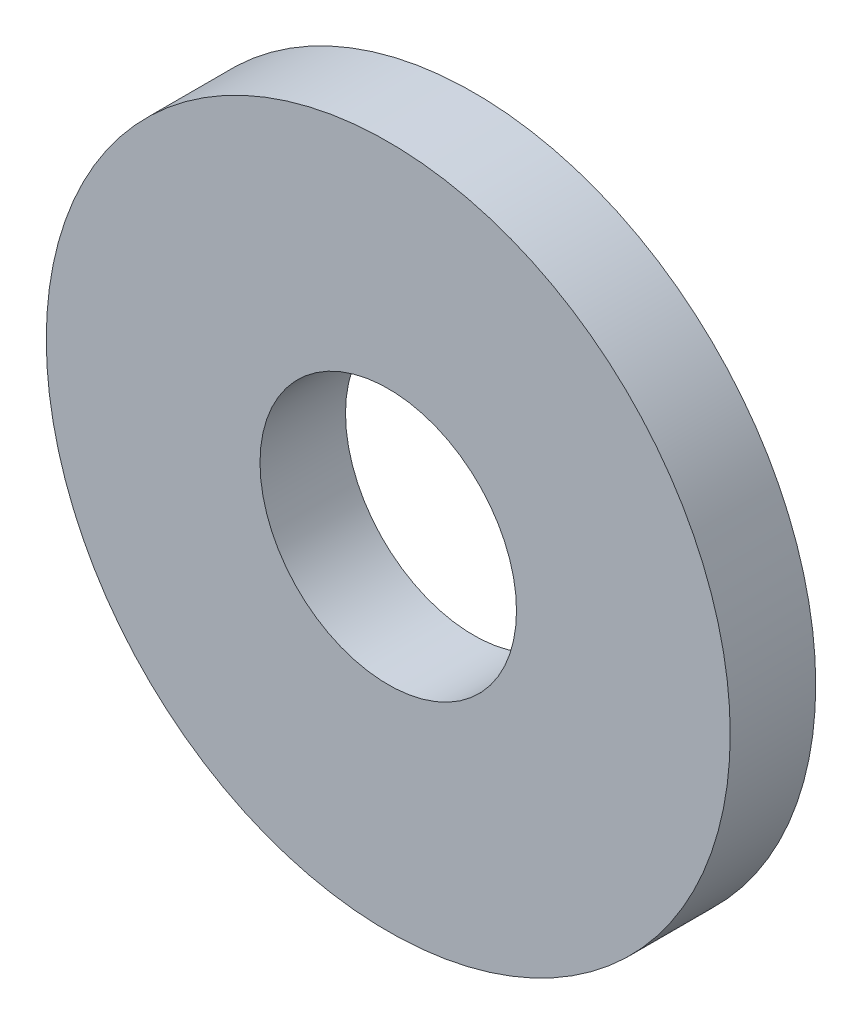
SolidWorks part; units mm, degrees
ref_plane "Alzado" through (0, 0, 0) normal (0, 0, 1) x (1, 0, 0)
ref_plane "Planta" through (0, 0, 0) normal (0, 1, 0) x (1, 0, 0)
ref_plane "Vista lateral" through (0, 0, 0) normal (1, 0, 0) x (0, 0, -1)
sketch "Croquis1" plane through (0, 0, 0) normal (0, 0, 1) x (1, 0, 0)
  circle A0 centre (0, 0) radius 4.7625
  circle A1 centre (0, 0) radius 12.7
  dimension "D1" = 9.525
  dimension "D2" = 25.4
extrude "Saliente-Extruir1" add sketch "Croquis1" along normal blind 3.175
